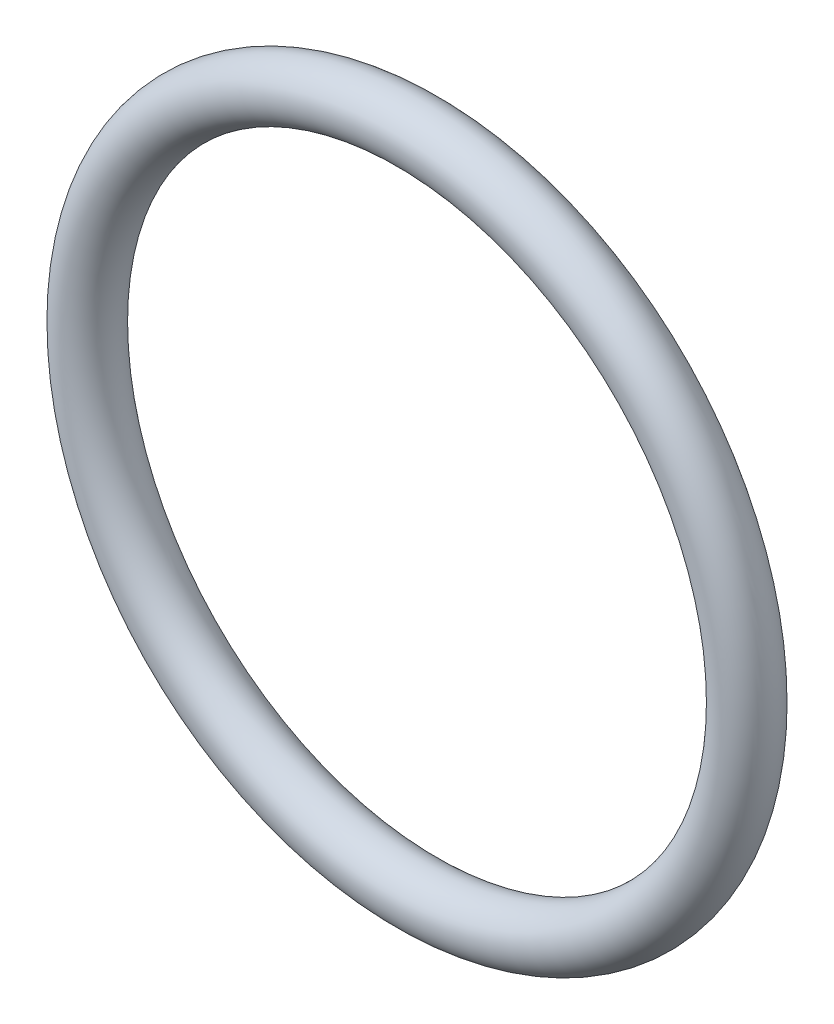
SolidWorks part; units mm, degrees
ref_plane "Front" through (0, 0, 0) normal (0, 0, 1) x (1, 0, 0)
ref_plane "Top" through (0, 0, 0) normal (0, 1, 0) x (1, 0, 0)
ref_plane "Right" through (0, 0, 0) normal (1, 0, 0) x (0, 0, -1)
sketch "Sketch1" plane through (0, 0, 0) normal (1, 0, 0) x (0, -1, 0)
  line L0 (0, -0.889) -> (0, 0.889) construction
  line L2 (-12.2796, 0) -> (12.2796, 0) construction
  line L3 (-9.3853, 0) -> (9.3853, 0) construction
  circle A0 centre (10.2743, 0) radius 0.889
  point P9 (9.3853, 0)
  point P10 (11.1633, 0)
  point P13 (10.2743, 0.889)
  point P14 (10.2743, -0.889)
  dimension "Width" = 1.778
  dimension "ID" = 18.7706
revolve "Revolve1" add sketch "Sketch1" angle 360 about L0
